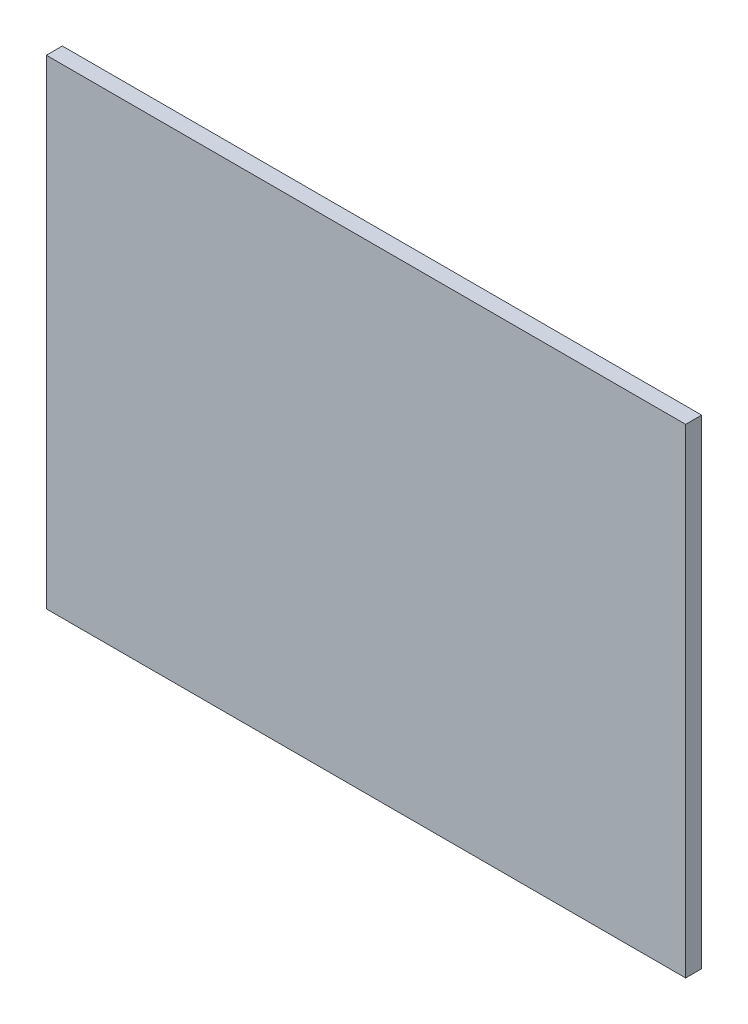
SolidWorks part; units mm, degrees
ref_plane "Ebene vorne" through (0, 0, 0) normal (0, 0, 1) x (1, 0, 0)
ref_plane "Ebene oben" through (0, 0, 0) normal (0, 1, 0) x (1, 0, 0)
ref_plane "Ebene rechts" through (0, 0, 0) normal (1, 0, 0) x (0, 0, -1)
sketch "Skizze1" plane through (0, 0, 0) normal (0, 0, 1) x (1, 0, 0)
  line L1 (-40, -30) -> (40, -30)
  line L2 (-40, -30) -> (-40, 30)
  line L3 (-40, 30) -> (40, 30)
  line L4 (40, -30) -> (40, 30)
  line L5 (-40, -30) -> (40, 30) construction
  line L6 (-40, 30) -> (40, -30) construction
  point P0 (0, 0)
  dimension "D1" = 80
  dimension "D2" = 60
extrude "Aufsatz-Linear austragen1" add sketch "Skizze1" along normal blind 2
